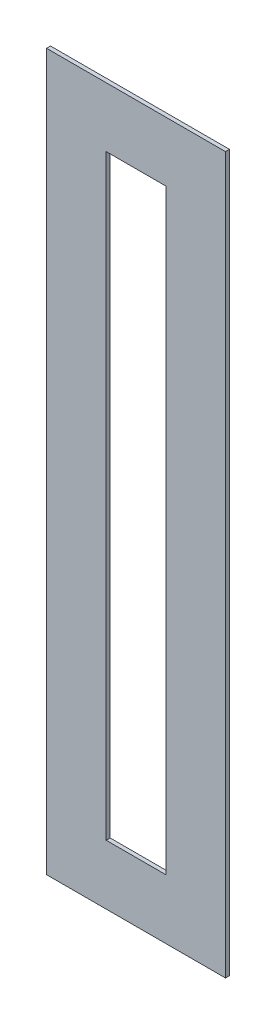
SolidWorks part; units mm, degrees
ref_plane "Front Plane" through (0, 0, 0) normal (0, 0, 1) x (1, 0, 0)
ref_plane "Top Plane" through (0, 0, 0) normal (0, 1, 0) x (1, 0, 0)
ref_plane "Right Plane" through (0, 0, 0) normal (1, 0, 0) x (0, 0, -1)
sketch "Sketch1" plane through (0, 0, 0) normal (0, 0, 1) x (1, 0, 0)
  line L0 (4.5, 18) -> (-4.5, 18)
  line L1 (1.5, 15) -> (-1.5, 15)
  line L2 (1.5, 15) -> (1.5, -15)
  line L3 (1.5, -15) -> (-1.5, -15)
  line L4 (-1.5, 15) -> (-1.5, -15)
  line L5 (1.5, 15) -> (-1.5, -15) construction
  line L6 (1.5, -15) -> (-1.5, 15) construction
  line L7 (-4.5, 18) -> (-4.5, -18)
  line L8 (4.5, -18) -> (-4.5, -18)
  line L9 (4.5, 18) -> (4.5, -18)
  point P0 (0, 0)
  dimension "D1" = 3
  dimension "D2" = 30
  dimension "D3" = 3
extrude "Boss-Extrude1" add sketch "Sketch1" along normal blind 0.2
